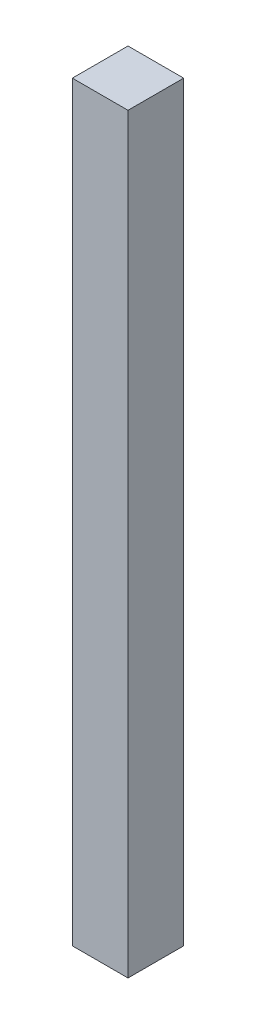
SolidWorks part; units mm, degrees
material "Plain Carbon Steel"
ref_plane "Front Plane" through (0, 0, 0) normal (0, 0, 1) x (1, 0, 0)
ref_plane "Top Plane" through (0, 0, 0) normal (0, 1, 0) x (1, 0, 0)
ref_plane "Right Plane" through (0, 0, 0) normal (1, 0, 0) x (0, 0, -1)
sketch "Sketch1" plane through (0, 0, 0) normal (0, 1, 0) x (1, 0, 0)
  line L1 (0, 0) -> (10, 0)
  line L2 (0, 0) -> (0, 10)
  line L3 (0, 10) -> (10, 10)
  line L4 (10, 0) -> (10, 10)
  dimension "D1" = 10
  dimension "D2" = 10
extrude "Boss-Extrude1" add sketch "Sketch1" along normal blind 135
